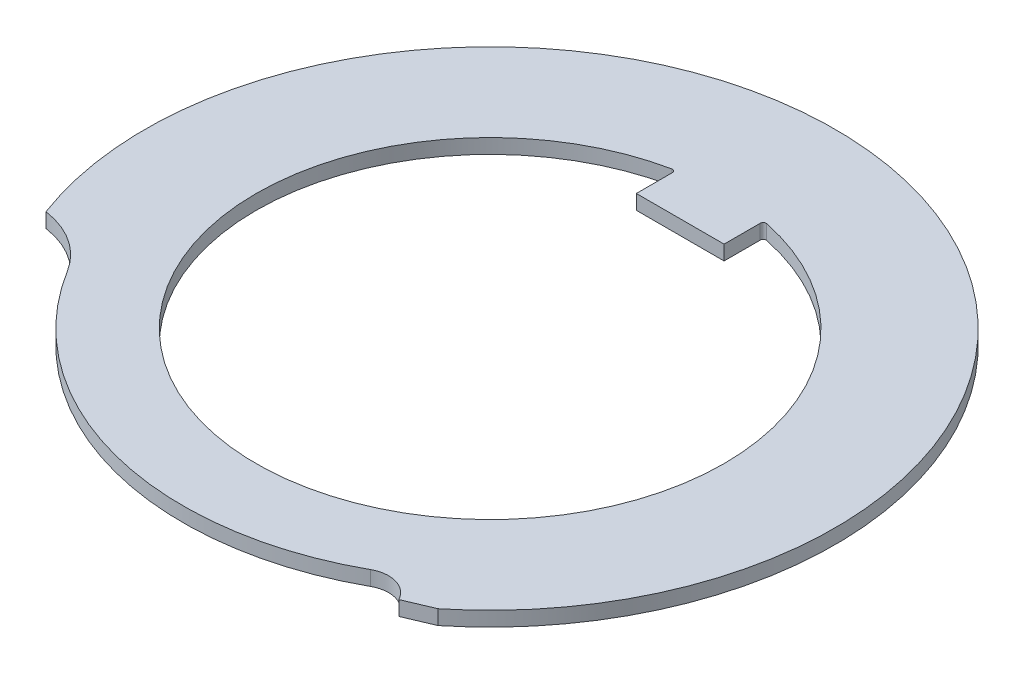
SolidWorks part; units mm, degrees
ref_plane "Front Plane" through (0, 0, 0) normal (0, 0, 1) x (1, 0, 0)
ref_plane "Top Plane" through (0, 0, 0) normal (0, 1, 0) x (1, 0, 0)
ref_plane "Right Plane" through (0, 0, 0) normal (1, 0, 0) x (0, 0, -1)
sketch "Sketch1" plane through (0, 0, 0) normal (0, 1, 0) x (1, 0, 0)
  line L0 (0, 11.8) -> (0, -10.5) construction
  line L1 (7.4058, -9.1866) -> (6.4656, -9.5857)
  line L2 (0, 0) -> (-11.0527, -4.1324) construction
  line L3 (0, 0) -> (6.4656, -9.5857) construction
  line L5 (0, 0) -> (11.8, 0) construction
  line L6 (-1.5, 6.5) -> (1.5, 6.5)
  line L7 (-1.5, 6.5) -> (-1.5, 7.8581)
  line L9 (1.5, 6.5) -> (1.5, 7.8581)
  line L10 (-1.5, 6.5) -> (0, 8) construction
  line L11 (0, 8) -> (1.5, 6.5) construction
  arc A0 (7.4058, -9.1866) -> (-11.0527, -4.1324) centre (0, 0) ccw
  arc A1 (-1.5, 7.8581) -> (1.5, 7.8581) centre (0, 0) ccw
  arc A2 (-8.9297, -5.5235) -> (5.0968, -9.18) centre (0, 0) ccw
  arc A3 (5.0968, -9.18) -> (6.4656, -9.5857) centre (5.5822, -10.0543) cw
  arc A4 (-11.0527, -4.1324) -> (-8.9297, -5.5235) centre (-11.4811, -7.1017) cw
  point P4 (0, 8)
  dimension "D1" = 23.6
  dimension "D2" = 16
  dimension "D3" = 21
  dimension "D6" = 1
  dimension "D7" = 3
  dimension "D4" = 146
  dimension "D5" = 103.5
  dimension "D9" = 11.35
  dimension "D8" = 23
  dimension "D10" = 6.5
  dimension "D11" = 3
extrude "Boss-Extrude1" add sketch "Sketch1" along normal blind 0.5
fillet "Fillet1" radius 0.1 2 edges at (-1.5, 0.25, -7.8581) (1.5, 0.25, -7.8581)
